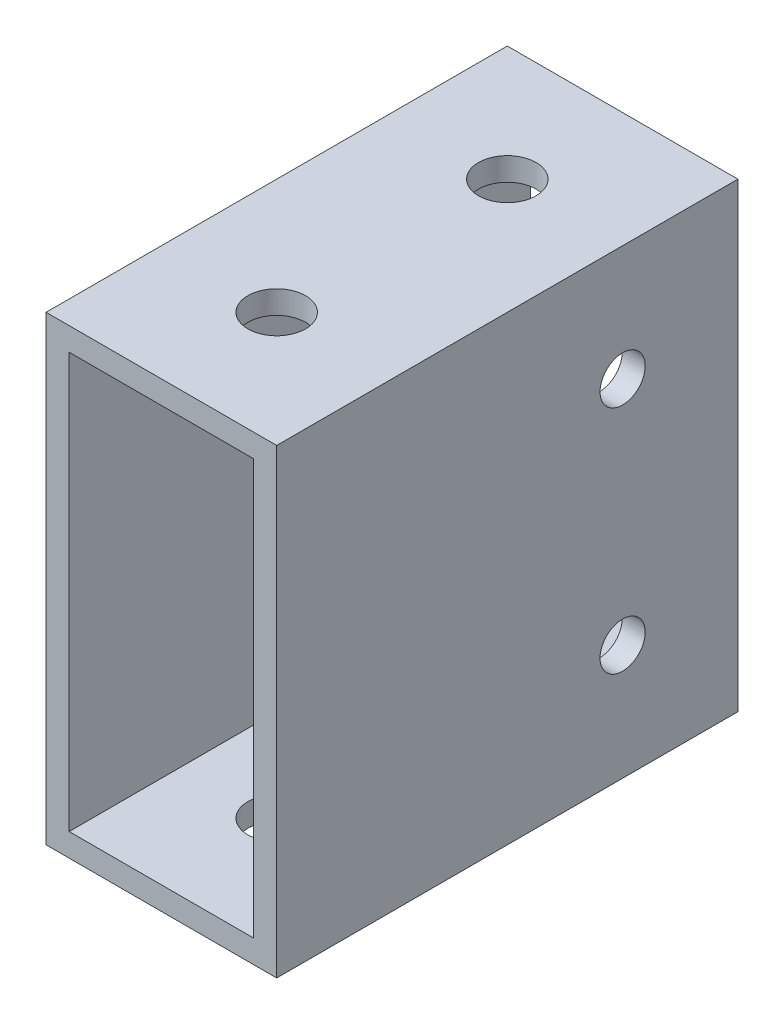
SolidWorks part; units mm, degrees
material "6061-T6 (SS)"
ref_plane "Front" through (0, 0, 0) normal (0, 0, 1) x (1, 0, 0)
ref_plane "Top" through (0, 0, 0) normal (0, 1, 0) x (1, 0, 0)
ref_plane "Right" through (0, 0, 0) normal (1, 0, 0) x (0, 0, -1)
sketch "Sketch1" plane through (0, 0, 0) normal (0, 0, 1) x (1, 0, 0)
  line L1 (-12.7, -25.4) -> (12.7, -25.4)
  line L2 (-12.7, -25.4) -> (-12.7, 25.4)
  line L3 (-12.7, 25.4) -> (12.7, 25.4)
  line L4 (12.7, -25.4) -> (12.7, 25.4)
  line L5 (-12.7, -25.4) -> (12.7, 25.4) construction
  line L6 (-12.7, 25.4) -> (12.7, -25.4) construction
  point P0 (0, 0)
  dimension "D1" = 50.8
  dimension "D2" = 25.4
extrude "Extrude-Thin1" add sketch "Sketch1" along normal mid plane 50.8 thin thin type one direction reverse wall 2.54
sketch "Sketch2" plane through (0, 25.4, 0) normal (0, 1, 0) x (1, 0, 0)
  line L0 (0, -25.4) -> (0, 25.4) construction
  line L1 (12.7, -25.4) -> (-12.7, -25.4) construction
  line L2 (12.7, 25.4) -> (-12.7, 25.4) construction
  circle A0 centre (0, 12.7) radius 3.175
  circle A1 centre (0, -12.7) radius 3.175
  dimension "D1" = 6.35
  dimension "D2" = 6.35
  dimension "D3" = 12.7
  dimension "D4" = 25.4
extrude "Cut-Extrude1" cut sketch "Sketch2" against normal through all
sketch "Sketch3" plane through (12.7, 0, 0) normal (1, 0, 0) x (0, 0, -1)
  line L0 (12.7, 25.4) -> (12.7, -25.4) construction
  line L2 (-25.4, -25.4) -> (25.4, -25.4) construction
  line L3 (25.4, -25.4) -> (25.4, 25.4) construction
  line L4 (-25.4, 25.4) -> (25.4, 25.4) construction
  circle A0 centre (12.7, 12.7) radius 2.4892
  circle A1 centre (12.7, -12.7) radius 2.4892
  dimension "D1" = 4.9784
  dimension "D2" = 25.4
  dimension "D3" = 12.7
  dimension "D4" = 12.7
extrude "Cut-Extrude2" cut sketch "Sketch3" against normal through all
